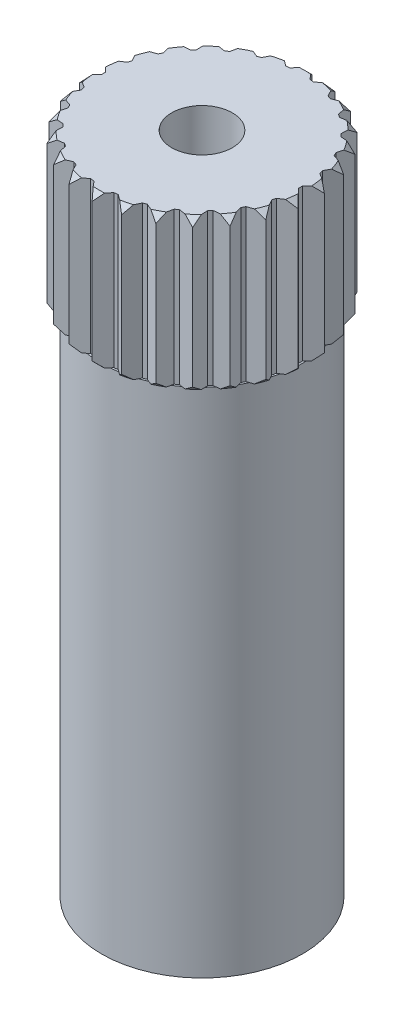
SolidWorks part; units mm, degrees
material "Brass"
ref_plane "Front Plane" through (0, 0, 0) normal (0, 0, 1) x (1, 0, 0)
ref_plane "Top Plane" through (0, 0, 0) normal (0, 1, 0) x (1, 0, 0)
ref_plane "Right Plane" through (0, 0, 0) normal (1, 0, 0) x (0, 0, -1)
sketch "Sketch12" plane through (0, 0, 0) normal (0, 1, 0) x (1, 0, 0)
  circle A0 centre (0, 0) radius 2.9
  dimension "D1" = 5.8
extrude "Boss-Extrude4" add sketch "Sketch12" along normal blind 13.5 separate body
sketch "Sketch13" plane through (0, 13.5, 0) normal (0, 1, 0) x (1, 0, 0)
  circle A2 centre (0, 0) radius 2.6
  circle A3 centre (0, 0) radius 2.9 construction
  dimension "D1" = 0.3
extrude "Boss-Extrude5" add sketch "Sketch13" along normal blind 4
sketch "Sketch14" plane through (0, 17.5, 0) normal (0, 1, 0) x (1, 0, 0)
  line L0 (0, 2.6) -> (0, 2.9) construction
  line L1 (0, 2.9) -> (-0.2629, 2.5867)
  line L2 (0, 2.9) -> (0.2629, 2.5867)
  line L3 (-0.2629, 2.5867) -> (0.2629, 2.5867) construction
  circle A0 centre (0, 0) radius 2.9 construction
  circle A1 centre (0, 0) radius 2.6
  arc A2 (0.2629, 2.5867) -> (-0.2629, 2.5867) centre (0, 0) ccw
  dimension "D2" = 80
  dimension "D3" = 0.5258
  dimension "D4" = 0.3
  dimension "D1" = 0
extrude "Boss-Extrude6" add sketch "Sketch14" against normal up to body (17.5 mm away)
pattern_circular "CirPattern1" count 26 over 360 about axis through (0, 0, 0) along (0, 1, 0) of "Boss-Extrude6"
sketch "Sketch15" plane through (0, 0, 0) normal (1, 0, 0) x (0, 0, -1)
  line L0 (2.9, 17.3232) -> (2.9, 17.5)
  line L1 (2.9, 13.5) -> (2.9, 17.5) construction
  line L2 (2.9, 17.5) -> (2.7232, 17.5)
  line L3 (2.1682, 17.5) -> (2.5678, 17.5) construction
  line L4 (2.7232, 17.5) -> (2.9, 17.3232)
  dimension "D1" = 45
  dimension "D2" = 0.25
revolve "Cut-Revolve1" cut sketch "Sketch15" angle 360 about axis through (0, 17.5, 0) along (0, -1, 0)
sketch "Sketch16" plane through (0, 17.5, 0) normal (0, 1, 0) x (1, 0, 0)
  circle A0 centre (0, 0) radius 0.8
  dimension "D1" = 1.6
extrude "Cut-Extrude1" cut sketch "Sketch16" against normal blind 4
ref_plane "Plane1" through (-0.3638, 13.5, -2.5744) normal (-0.9902, 0, 0.1399) x (0.1399, 0, 0.9902)
sketch "Sketch17" plane through (0, 0, 0) normal (0, 0, 1) x (1, 0, 0)
  line L0 (2.9, 0) -> (2.65, 0)
  line L1 (-2.9, 0) -> (2.9, 0) construction
  line L2 (2.65, 0) -> (2.65, 13.5)
  line L3 (2.65, 13.5) -> (2.9, 13.5)
  line L4 (2.9, 13.5) -> (2.9, 0)
  line L5 (0, 0) -> (2.65, 0) construction
  line L6 (2.7115, 13.5) -> (2.3254, 13.5) construction
  dimension "D1" = 0.25
  dimension "D2" = 2.65
  dimension "D3" = 2.9
revolve "Cut-Revolve2" cut sketch "Sketch17" angle 360 about axis through (0, 13.5, 0) along (0, -1, 0)
ref_plane "Plane2" through (0, 15.5, 0) normal (0, 1, 0) x (1, 0, 0)
mirror "Mirror1" about plane through (0, 15.5, 0) normal (0, 1, 0) of "Cut-Revolve1"
